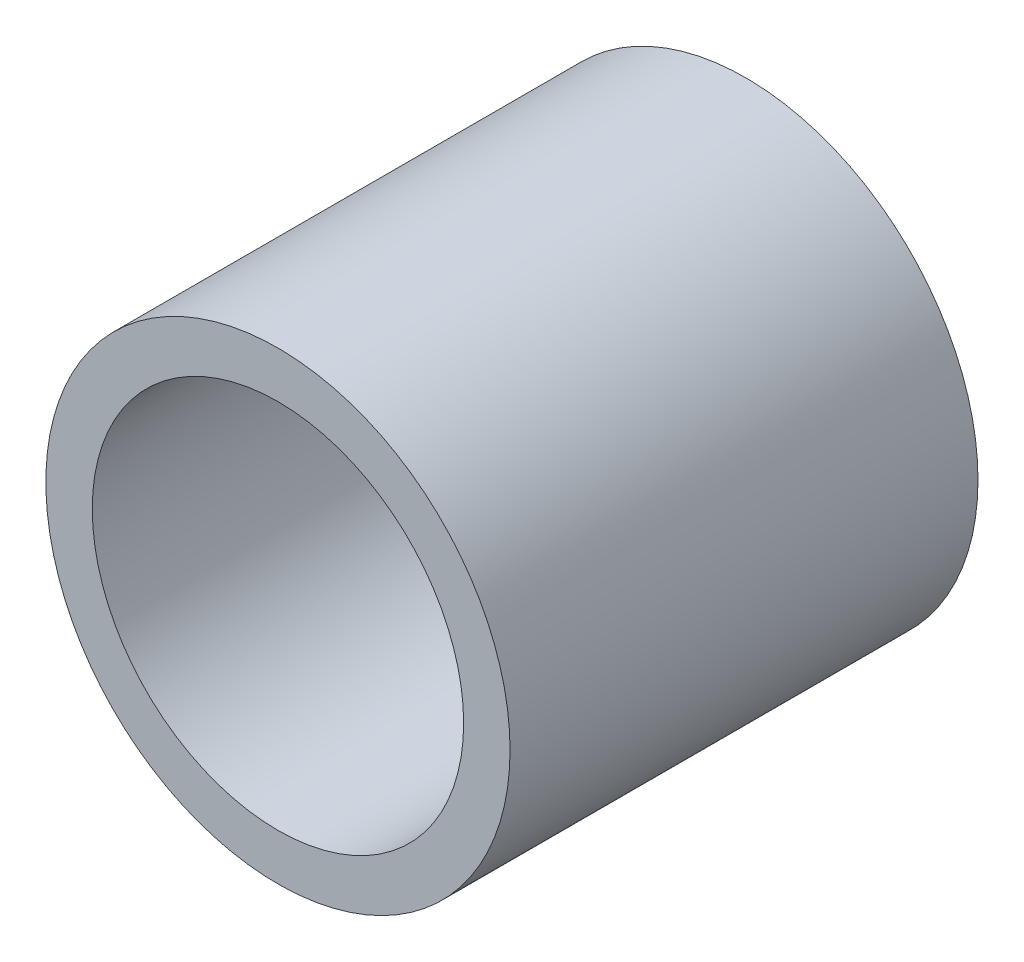
SolidWorks part; units mm, degrees
material "Plain Carbon Steel"
ref_plane "Front Plane" through (0, 0, 0) normal (0, 0, 1) x (1, 0, 0)
ref_plane "Top Plane" through (0, 0, 0) normal (0, 1, 0) x (1, 0, 0)
ref_plane "Right Plane" through (0, 0, 0) normal (1, 0, 0) x (0, 0, -1)
sketch "Sketch1" plane through (0, 0, 0) normal (0, 0, 1) x (1, 0, 0)
  circle A0 centre (0, 0) radius 7.9375
  circle A1 centre (0, 0) radius 6.35
  dimension "D1" = 15.875
  dimension "D2" = 12.7
extrude "Boss-Extrude1" add sketch "Sketch1" along normal mid plane 16.002
